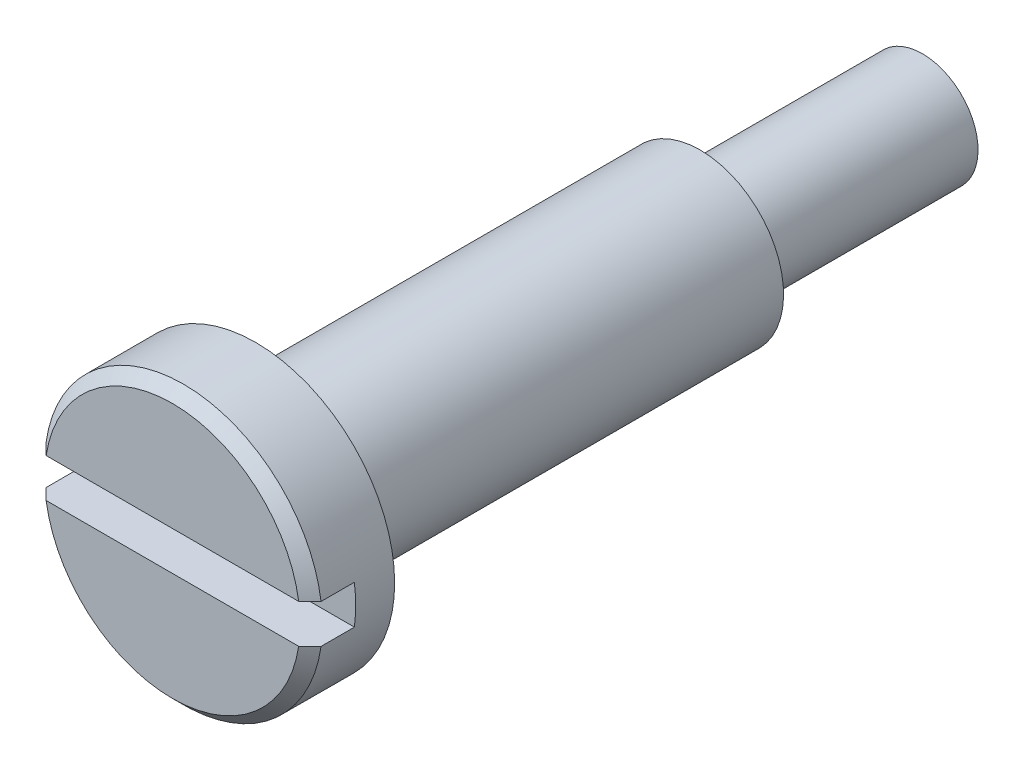
SolidWorks part; units mm, degrees
material "AISI 304"
ref_plane "前视基准面" through (0, 0, 0) normal (0, 0, 1) x (1, 0, 0)
ref_plane "上视基准面" through (0, 0, 0) normal (0, 1, 0) x (1, 0, 0)
ref_plane "右视基准面" through (0, 0, 0) normal (1, 0, 0) x (0, 0, -1)
sketch "草图1" plane through (0, 0, 0) normal (1, 0, 0) x (0, 0, -1)
  line L0 (0, 0) -> (0, 2.5)
  line L1 (0, 2.5) -> (1.5, 2.5)
  line L2 (1.5, 2.5) -> (1.5, 1.5)
  line L3 (1.5, 1.5) -> (9.5, 1.5)
  line L4 (9.5, 1.5) -> (9.5, 0.7)
  line L5 (9.5, 0.7) -> (9.8, 0.7)
  line L6 (9.8, 0.7) -> (9.8, 1)
  line L7 (9.8, 1) -> (13.5, 1)
  line L8 (13.5, 1) -> (13.5, 0)
  line L9 (13.5, 0) -> (0, 0) construction
  line L10 (0, 0) -> (13.5, 0)
  dimension "光杆直径" = 3
  dimension "dk" = 5
  dimension "k" = 1.5
  dimension "公称直径" = 2
  dimension "螺纹长度" = 4
  dimension "光杆长度" = 8
  dimension "D7" = 0.3
  dimension "D8" = 0.3
revolve "旋转1" add sketch "草图1" angle 360 about L9
sketch "草图2" plane through (0, 0, 0) normal (1, 0, 0) x (0, 0, -1)
  line L1 (-0.8, -0.35) -> (0.8, -0.35)
  line L2 (-0.8, -0.35) -> (-0.8, 0.35)
  line L3 (-0.8, 0.35) -> (0.8, 0.35)
  line L4 (0.8, -0.35) -> (0.8, 0.35)
  line L5 (0, 0.35) -> (0, -0.35) construction
  line L6 (-0.8, 0) -> (0.8, 0) construction
  point P0 (0, 0)
  dimension "n" = 0.8
  dimension "t" = 0.7
extrude "切除-拉伸1" cut sketch "草图2" against normal through all both and the other way through all
chamfer "倒角1" distance 0.2 angle 45 2 edges at (0, 2.5, 0) (0, -2.5, 0)
